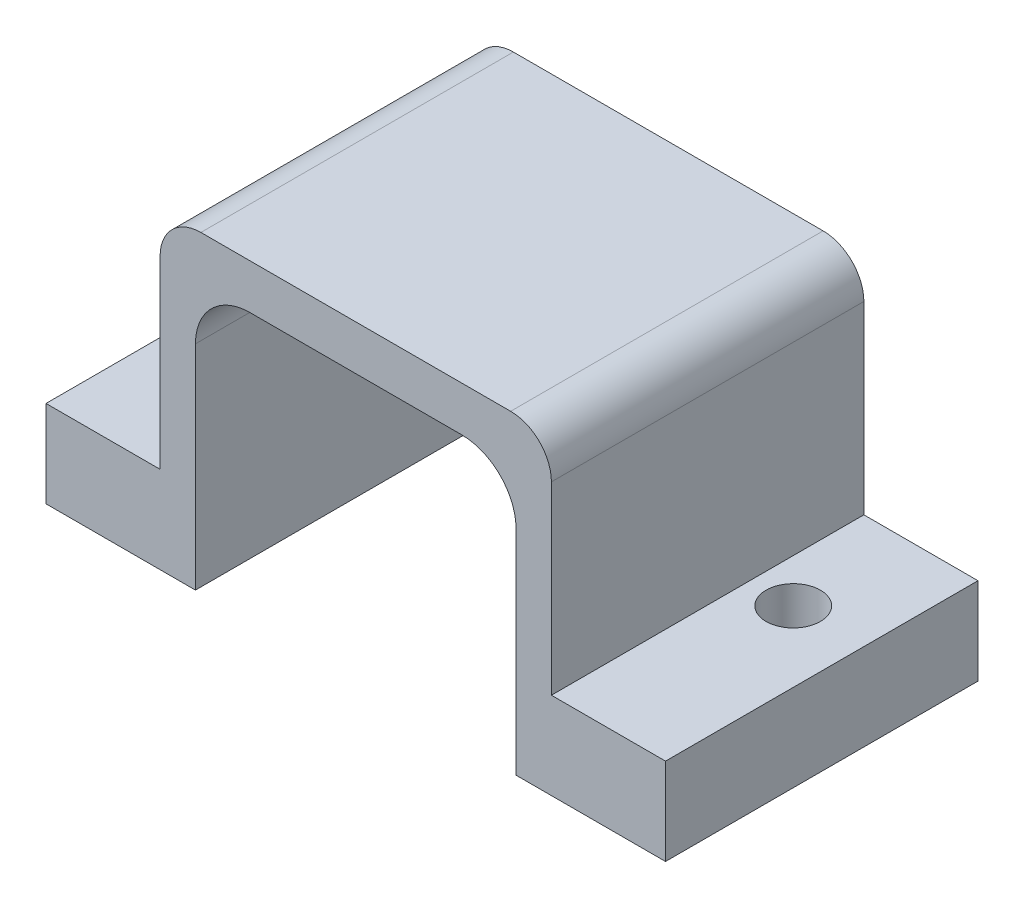
SolidWorks part; units mm, degrees
ref_plane "前视基准面" through (0, 0, 0) normal (0, 0, 1) x (1, 0, 0)
ref_plane "上视基准面" through (0, 0, 0) normal (0, 1, 0) x (1, 0, 0)
ref_plane "右视基准面" through (0, 0, 0) normal (1, 0, 0) x (0, 0, -1)
sketch "草图1" plane through (0, 0, 0) normal (0, 0, 1) x (1, 0, 0)
  line L0 (0, 0) -> (0, 9.85)
  line L1 (0, 9.85) -> (11.8, 9.85)
  line L2 (11.8, 9.85) -> (11.8, 0)
  line L3 (11.8, 0) -> (17.3, 0)
  line L4 (17.3, 0) -> (17.3, 3.2)
  line L5 (17.3, 3.2) -> (13.1, 3.2)
  line L6 (13.1, 3.2) -> (13.1, 11.5)
  line L7 (13.1, 11.5) -> (-1.3, 11.5)
  line L8 (-1.3, 11.5) -> (-1.3, 3.2)
  line L9 (-1.3, 3.2) -> (-5.5, 3.2)
  line L10 (-5.5, 3.2) -> (-5.5, 0)
  line L11 (-5.5, 0) -> (0, 0)
  dimension "D1" = 11.8
  dimension "D2" = 14.4
  dimension "D3" = 1.3
  dimension "D4" = 3.2
  dimension "D5" = 3.2
  dimension "D6" = 11.5
  dimension "D7" = 9.85
  dimension "D8" = 5.5
  dimension "D9" = 5.5
extrude "凸台-拉伸1" add sketch "草图1" along normal blind 11.5
fillet "圆角1" radius 2 2 edges at (11.8, 9.85, 5.75) (0, 9.85, 5.75)
fillet "圆角2" radius 1.5 2 edges at (13.1, 11.5, 5.75) (-1.3, 11.5, 5.75)
sketch "草图2" plane through (0, 3.2, 0) normal (0, 1, 0) x (1, 0, 0)
  line L4 (-1.3, 0) -> (-5.5, 0)
  line L5 (-5.5, 0) -> (-5.5, -11.5)
  line L6 (-5.5, -11.5) -> (-1.3, -11.5)
  line L7 (-1.3, -11.5) -> (-1.3, 0)
  line L8 (-1.3, 0) -> (-5.5, 0)
  line L9 (-5.5, 0) -> (-5.5, -11.5)
  line L10 (-5.5, -11.5) -> (-1.3, -11.5)
  line L11 (-1.3, -11.5) -> (-1.3, 0)
  circle A0 centre (-2.9, -4.2) radius 1
  circle A1 centre (14.7, -4.2) radius 1
  point P12 (-3.2083, -4.409)
  dimension "D5" = 2
  dimension "D6" = 2
  dimension "D2" = 4.2
  dimension "D3" = 17.6
  dimension "D4" = 1.6
  dimension "D1" = 0
extrude "切除-拉伸1" cut sketch "草图2" against normal blind 11.5 contours A0 | A1
